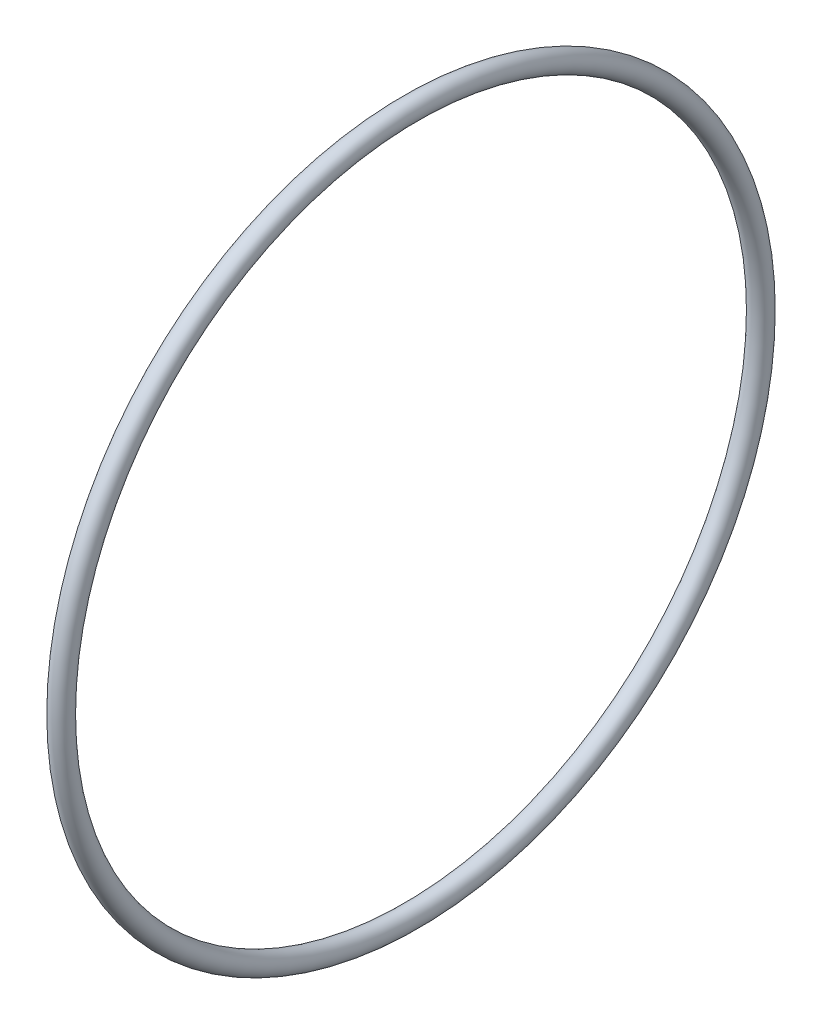
SolidWorks part; units mm, degrees
ref_plane "Front Plane" through (0, 0, 0) normal (0, 0, 1) x (1, 0, 0)
ref_plane "Top Plane" through (0, 0, 0) normal (0, 1, 0) x (1, 0, 0)
ref_plane "Right Plane" through (0, 0, 0) normal (1, 0, 0) x (0, 0, -1)
sketch "Sketch2" plane through (0, 0, 0) normal (0, 0, 1) x (1, 0, 0)
  line L0 (0, 0) -> (58.591, 0) construction
  line L2 (0, 0) -> (18.4, 0)
  line L3 (0, 0) -> (0, 2.5)
  line L4 (0, 2.5) -> (18.4, 2.5)
  line L5 (18.4, 0) -> (18.4, 2.5)
  line L6 (6.0094, 2.5) -> (6.0094, 6)
  line L11 (6.0094, 6) -> (9.9794, 6)
  line L16 (12.9794, 6) -> (12.9794, 3)
  line L17 (12.9794, 3) -> (13.6398, 3)
  line L18 (13.6398, 3) -> (13.6398, 2.5)
  line L19 (13.6398, 2.5) -> (6.0094, 2.5)
  line L22 (13.6398, 2.5) -> (16.1198, 2.5)
  line L23 (13.6398, 2.5) -> (13.6398, 4)
  line L24 (13.6398, 4) -> (16.1198, 4)
  line L25 (16.1198, 2.5) -> (16.1198, 4)
  line L27 (6.0094, 6) -> (9.9794, 6)
  line L28 (6.0094, 6) -> (6.0094, 9)
  line L29 (6.0094, 9) -> (9.9794, 9)
  line L30 (9.9794, 6) -> (9.9794, 9)
  line L31 (6.0094, 9) -> (6.0094, 8.25)
  line L32 (6.0094, 8.25) -> (5.0094, 8.25)
  line L33 (8.6609, 22.001) -> (8.6609, 12.476) construction
  line L34 (5.0094, 12.476) -> (12.3124, 12.476)
  line L35 (9.9794, 9) -> (12.3124, 9)
  line L36 (5.0094, 7.9375) -> (1.7709, 7.9375)
  line L37 (5.0094, 8.25) -> (5.0094, 12.476)
  line L38 (5.0094, 7.9375) -> (5.0094, 13.9365)
  line L39 (5.0094, 13.9365) -> (1.7709, 13.9365)
  line L40 (1.7709, 7.9375) -> (1.7709, 13.9365)
  line L41 (5.0094, 22.001) -> (12.3124, 22.001)
  line L42 (5.0094, 22.001) -> (5.0094, 30.1625)
  line L43 (5.0094, 30.1625) -> (12.3124, 30.1625)
  line L44 (12.3124, 22.001) -> (12.3124, 30.1625)
  line L49 (16.6398, 22.001) -> (16.6398, 7.5)
  line L51 (23.0198, 7.5) -> (23.0198, 6.5)
  line L54 (16.1198, 4) -> (13.6398, 4)
  line L56 (18.0398, 7.5) -> (23.0198, 7.5)
  line L57 (13.3124, 22.001) -> (16.6398, 22.001)
  line L58 (16.1198, 3.5) -> (20.0198, 3.5)
  line L59 (29.9098, 14) -> (26.9098, 11)
  line L60 (4.0094, 31.75) -> (18.0398, 31.75)
  line L61 (18.0398, 7.5) -> (23.0198, 7.5)
  line L62 (18.0398, 7.5) -> (18.0398, 12)
  line L63 (18.0398, 12) -> (23.0198, 12)
  line L64 (23.0198, 7.5) -> (23.0198, 12)
  line L65 (18.0398, 31.75) -> (18.0398, 12)
  line L66 (23.0198, 11) -> (26.9098, 11)
  line L67 (34.8098, 23) -> (31.3098, 19.5)
  line L68 (35.8098, 31) -> (38.7998, 33.99)
  line L69 (29.9098, 14) -> (29.9098, 15)
  line L70 (29.9098, 15) -> (22.9398, 15)
  line L71 (22.9398, 15) -> (21.0398, 15)
  line L72 (18.0398, 7.5) -> (16.6398, 7.5)
  line L73 (21.0398, 15) -> (21.0398, 43)
  line L74 (19.6115, 40) -> (9.6516, 40)
  line L75 (9.6516, 40) -> (4.0094, 40)
  line L76 (21.0398, 43) -> (19.6115, 43)
  line L77 (22.9398, 15) -> (29.9098, 15)
  line L78 (22.9398, 15) -> (22.9398, 21)
  line L79 (22.9398, 21) -> (29.9098, 21)
  line L80 (29.9098, 15) -> (29.9098, 21)
  line L81 (9.6516, 40) -> (19.6115, 40)
  line L82 (9.6516, 40) -> (9.6516, 50)
  line L83 (9.6516, 50) -> (19.6115, 50)
  line L84 (19.6115, 40) -> (19.6115, 50)
  line L85 (4.0094, 40) -> (4.0094, 31.75)
  line L86 (12.9794, 3) -> (12.9794, 2.5)
  line L87 (31.3098, 19.5) -> (29.9098, 19.5)
  line L88 (21.4694, 63.5) -> (21.4694, 51.308)
  line L89 (21.4694, 63.5) -> (25.9398, 63.5)
  line L90 (25.9398, 63.5) -> (25.9398, 25)
  line L91 (27.8398, 25) -> (25.9398, 25)
  line L92 (9.6516, 48) -> (8.2233, 48)
  line L93 (8.2233, 48) -> (8.2233, 53.476)
  line L94 (8.2233, 53.476) -> (19.6115, 53.476)
  line L95 (19.6115, 53.476) -> (19.6115, 50)
  line L96 (13.9174, 63.001) -> (13.9174, 53.476) construction
  line L97 (8.2233, 63.001) -> (19.6115, 63.001)
  line L98 (8.2233, 63.001) -> (8.2233, 68.2625)
  line L99 (8.2233, 68.2625) -> (19.6115, 68.2625)
  line L100 (19.6115, 63.001) -> (19.6115, 68.2625)
  line L101 (12.9794, 6) -> (11.9794, 6)
  line L102 (8.2233, 44.825) -> (4.9848, 44.825)
  line L103 (8.2233, 44.825) -> (8.2233, 54.9365)
  line L104 (8.2233, 54.9365) -> (4.9848, 54.9365)
  line L106 (9.9794, 6) -> (10.8794, 6)
  line L107 (27.8398, 25) -> (34.8098, 25)
  line L108 (34.8098, 25) -> (34.8098, 23)
  line L109 (0, 0) -> (-2, 0)
  line L110 (0, 0) -> (0, 11)
  line L111 (27.8398, 25) -> (34.8098, 25)
  line L112 (27.8398, 25) -> (27.8398, 32.5)
  line L113 (27.8398, 32.5) -> (34.8098, 32.5)
  line L114 (34.8098, 25) -> (34.8098, 32.5)
  line L115 (35.8098, 31) -> (34.8098, 31)
  line L116 (27.8398, 32.5) -> (27.8398, 64.5)
  line L117 (20.5849, 74.025) -> (6.2499, 74.025)
  line L118 (6.2499, 74.025) -> (6.2499, 76.2)
  line L119 (38.7998, 47.29) -> (30.8398, 55.25)
  line L120 (0, 11) -> (-2, 11)
  line L121 (38.7998, 43.815) -> (30.8623, 43.815)
  line L123 (-4.8152, 69.85) -> (1.5348, 76.2)
  line L124 (38.7998, 47.29) -> (38.7998, 33.99)
  line L125 (-2, 0) -> (-2, 11)
  line L126 (38.7998, 37.465) -> (30.8623, 37.465)
  line L127 (30.8623, 43.815) -> (30.8623, 37.465)
  line L128 (6.0094, 2.5) -> (6.0094, 0)
  line L129 (-0.0152, 63.5) -> (-0.0152, 30)
  line L132 (4.9848, 63.5) -> (-0.0152, 63.5)
  line L136 (-1.8152, 30) -> (-11.7752, 30)
  line L138 (-13.7752, 25.4) -> (-2, 25.4)
  line L139 (-2, 25.4) -> (-2, 11.5)
  line L140 (27.8398, 64.5) -> (20.5849, 64.5)
  line L141 (-1.8152, 30) -> (-11.7752, 30)
  line L142 (-1.8152, 30) -> (-1.8152, 39)
  line L143 (-1.8152, 39) -> (-11.7752, 39)
  line L144 (-11.7752, 30) -> (-11.7752, 39)
  line L145 (20.5849, 64.5) -> (20.5849, 74.025)
  line L146 (-12.7752, 37) -> (-12.7752, 47.29)
  line L147 (-12.7752, 37) -> (-11.7752, 37)
  line L148 (30.8398, 55.25) -> (30.8398, 76.2)
  line L149 (11.9794, 6) -> (11.9794, 5.45)
  line L154 (-2, 11.5) -> (0.5, 11.5)
  line L155 (4.9848, 60.6197) -> (24.0348, 60.6197)
  line L160 (4.9848, 60.6197) -> (4.9848, 55.8572)
  line L161 (4.9848, 55.8572) -> (24.0348, 55.8572)
  line L166 (24.0348, 60.6197) -> (24.0348, 55.8572)
  line L167 (4.9848, 60.6197) -> (24.0348, 55.8572) construction
  line L172 (4.9848, 55.8572) -> (24.0348, 60.6197) construction
  line L173 (24.0348, 62.2072) -> (25.9398, 62.2072)
  line L174 (11.9794, 5.45) -> (10.8794, 5.45)
  line L175 (10.8794, 6) -> (10.8794, 5.45)
  line L176 (24.0348, 62.2072) -> (24.0348, 54.2697)
  line L177 (24.0348, 54.2697) -> (25.9398, 54.2697)
  line L178 (25.9398, 62.2072) -> (25.9398, 54.2697)
  line L179 (24.0348, 62.2072) -> (25.9398, 54.2697) construction
  line L180 (24.0348, 54.2697) -> (25.9398, 62.2072) construction
  line L181 (3, 19.6197) -> (15.7, 19.6197)
  line L182 (3, 19.6197) -> (3, 14.8572)
  line L183 (3, 14.8572) -> (15.7, 14.8572)
  line L184 (15.7, 19.6197) -> (15.7, 14.8572)
  line L185 (3, 19.6197) -> (15.7, 14.8572) construction
  line L186 (3, 14.8572) -> (15.7, 19.6197) construction
  line L187 (15.7, 21.2072) -> (16.6398, 21.2072)
  line L188 (15.7, 21.2072) -> (15.7, 13.2697)
  line L189 (15.7, 13.2697) -> (16.6398, 13.2697)
  line L190 (16.6398, 21.2072) -> (16.6398, 13.2697)
  line L191 (15.7, 21.2072) -> (16.6398, 13.2697) construction
  line L192 (15.7, 13.2697) -> (16.6398, 21.2072) construction
  line L193 (0.5, 11.5) -> (0.5, 6.9375)
  line L194 (0.5, 6.9375) -> (1.7709, 6.9375)
  line L195 (23.0198, 6.5) -> (20.0198, 3.5)
  line L196 (4.9848, 63.5) -> (4.9848, 54.9365)
  line L197 (3, 43.825) -> (4.9848, 43.825)
  line L198 (1.7709, 6.9375) -> (1.7709, 7.9375)
  line L199 (6.0094, 0) -> (12.9794, 0)
  line L200 (12.9794, 0) -> (12.9794, 2.5)
  line L201 (18.0398, 31.75) -> (18.0398, 35.875)
  line L202 (18.0398, 35.875) -> (21.0398, 35.875)
  line L203 (30.8398, 76.2) -> (6.2499, 76.2)
  line L204 (2.8049, 69.85) -> (7.2499, 69.85) construction
  line L205 (7.2499, 67.4688) -> (26.2999, 67.4688)
  line L206 (7.2499, 74.025) -> (7.2499, 64.5)
  line L207 (7.2499, 64.5) -> (-1.8152, 64.5)
  line L208 (-1.8152, 64.5) -> (-1.8152, 39)
  line L209 (-12.7752, 47.29) -> (-4.8152, 55.25)
  line L210 (-4.8152, 55.25) -> (-4.8152, 69.85)
  line L211 (7.2499, 67.4688) -> (7.2499, 72.2312)
  line L212 (7.2499, 72.2312) -> (26.2999, 72.2313)
  line L213 (26.2999, 67.4688) -> (26.2999, 72.2313)
  line L214 (26.2999, 73.8187) -> (30.8398, 73.8187)
  line L215 (26.2999, 73.8187) -> (26.2999, 65.8813)
  line L216 (26.2999, 65.8813) -> (30.8398, 65.8813)
  line L217 (30.8398, 73.8187) -> (30.8398, 65.8813)
  line L218 (2.8049, 72.2313) -> (25.0299, 72.2313)
  line L219 (2.8049, 72.2313) -> (2.8049, 67.4687)
  line L220 (2.8049, 67.4687) -> (25.0299, 67.4687)
  line L221 (25.0299, 72.2313) -> (25.0299, 67.4687)
  line L222 (25.0299, 69.85) -> (20.5849, 69.85) construction
  line L223 (21.4694, 51.308) -> (22.9398, 51.308)
  line L224 (22.9398, 51.308) -> (22.9398, 21)
  line L225 (13.6398, 4) -> (13.6398, 12.2697)
  line L226 (13.6398, 12.2697) -> (13.3124, 12.2697)
  line L227 (13.3124, 12.2697) -> (13.3124, 22.001)
  line L228 (12.3124, 9) -> (12.3124, 12.476)
  line L229 (-1.8152, 30) -> (-0.0152, 30)
  line L230 (8.2233, 65.6317) -> (2.8049, 65.6317) construction
  line L231 (19.6115, 65.6317) -> (25.0299, 65.6317) construction
  line L232 (1.5348, 76.2) -> (6.2499, 76.2)
  line L233 (-11.7752, 30) -> (-13.7752, 30)
  line L234 (-13.7752, 30) -> (-13.7752, 25.4)
  line L235 (3, 13.9365) -> (3, 43.825)
  line L236 (4.9848, 54.9365) -> (4.9848, 44.825)
  line L237 (4.9848, 43.825) -> (4.9848, 44.825)
  circle A0 centre (26.8898, 25.95) radius 0.95
  circle A1 centre (21.9898, 15.95) radius 0.95
  circle A2 centre (17.3398, 8.2) radius 0.7
  circle A3 centre (10.4294, 6.45) radius 0.45
  circle A4 centre (-0.9152, 30.9) radius 0.9
  point P7 (24.9873, 58.2385)
  point P131 (16.1699, 17.2385)
  point P135 (14.5098, 58.2385)
  point P146 (9.35, 17.2385)
sketch "Sketch3" plane through (0, 0, 0) normal (0, 0, 1) x (1, 0, 0)
  circle A0 centre (-0.9152, 30.9) radius 0.9 construction
  circle A1 centre (-0.9152, 30.9) radius 0.9
revolve "Revolve1" add sketch "Sketch3" angle 360 about L0
